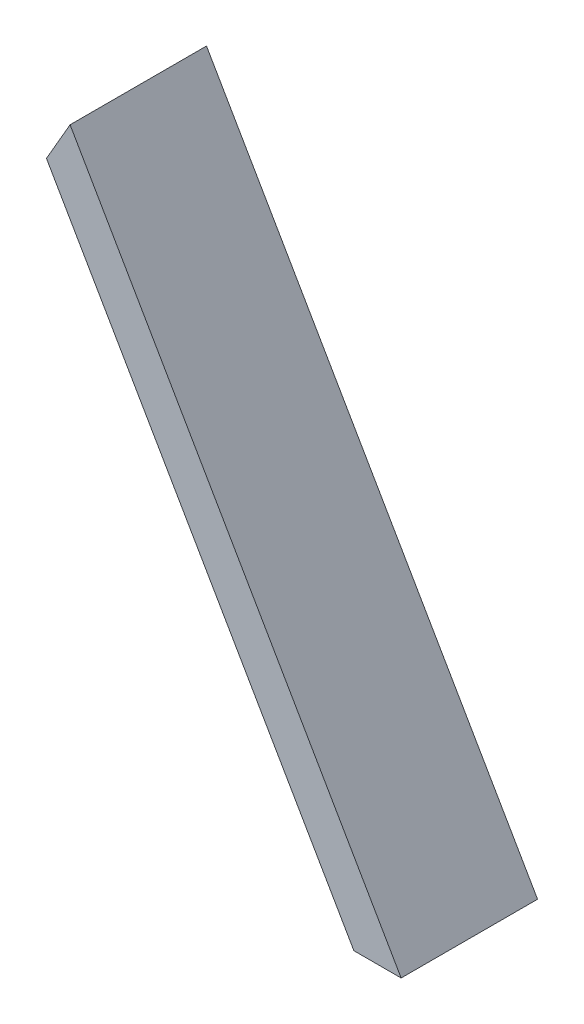
SolidWorks part; units mm, degrees
ref_plane "Front Plane" through (0, 0, 0) normal (0, 0, 1) x (1, 0, 0)
ref_plane "Top Plane" through (0, 0, 0) normal (0, 1, 0) x (1, 0, 0)
ref_plane "Right Plane" through (0, 0, 0) normal (1, 0, 0) x (0, 0, -1)
sketch "Sketch2" plane through (0, 0, 0) normal (0, 0, 1) x (1, 0, 0)
  line L0 (82.55, -133.4558) -> (-71.5515, 133.4558)
  line L1 (60.553, -133.4558) -> (-82.55, 114.4058)
  line L2 (82.55, -133.4558) -> (60.553, -133.4558)
  line L3 (-71.5515, 133.4558) -> (-82.55, 114.4058)
  dimension "D1" = 19.05
extrude "Boss-Extrude1" add sketch "Sketch2" along normal blind 63.5
